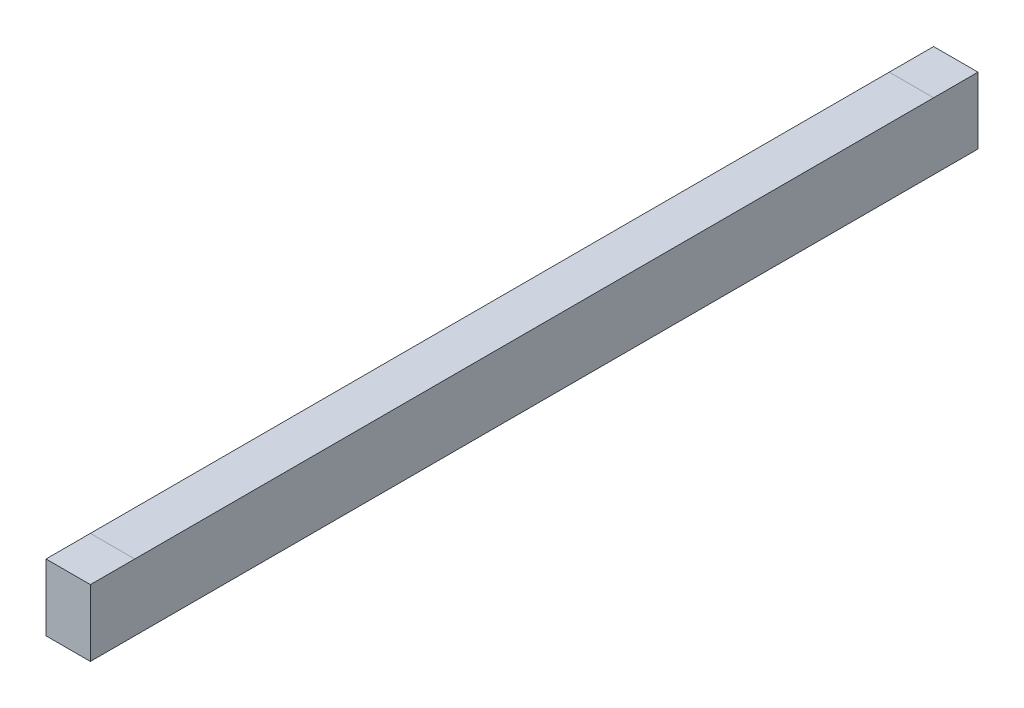
SolidWorks part; units mm, degrees
ref_plane "Front Plane" through (0, 0, 0) normal (0, 0, 1) x (1, 0, 0)
ref_plane "Top Plane" through (0, 0, 0) normal (0, 1, 0) x (1, 0, 0)
ref_plane "Right Plane" through (0, 0, 0) normal (1, 0, 0) x (0, 0, -1)
sketch "Sketch1" plane through (0, 0, 0) normal (0, 0, 1) x (1, 0, 0)
  line L1 (0, 0) -> (100, 0)
  line L2 (0, 0) -> (0, 150)
  line L3 (0, 150) -> (100, 150)
  line L4 (100, 0) -> (100, 150)
  dimension "D1" = 150
  dimension "D2" = 100
extrude "Boss-Extrude1" add sketch "Sketch1" along normal blind 2000
sketch "Szkic1" plane through (0, 150, 0) normal (0, 1, 0) x (1, 0, 0)
  line L0 (0, -1900) -> (100, -1900)
  line L1 (100, -2000) -> (100, 0) construction
  line L2 (0, -2000) -> (0, 0) construction
  line L3 (100, -2000) -> (0, -2000) construction
  line L4 (0, -100) -> (100, -100)
  line L5 (100, 0) -> (0, 0) construction
  dimension "D1" = 100
  dimension "D2" = 100
split line "Linia podziałowa1"
